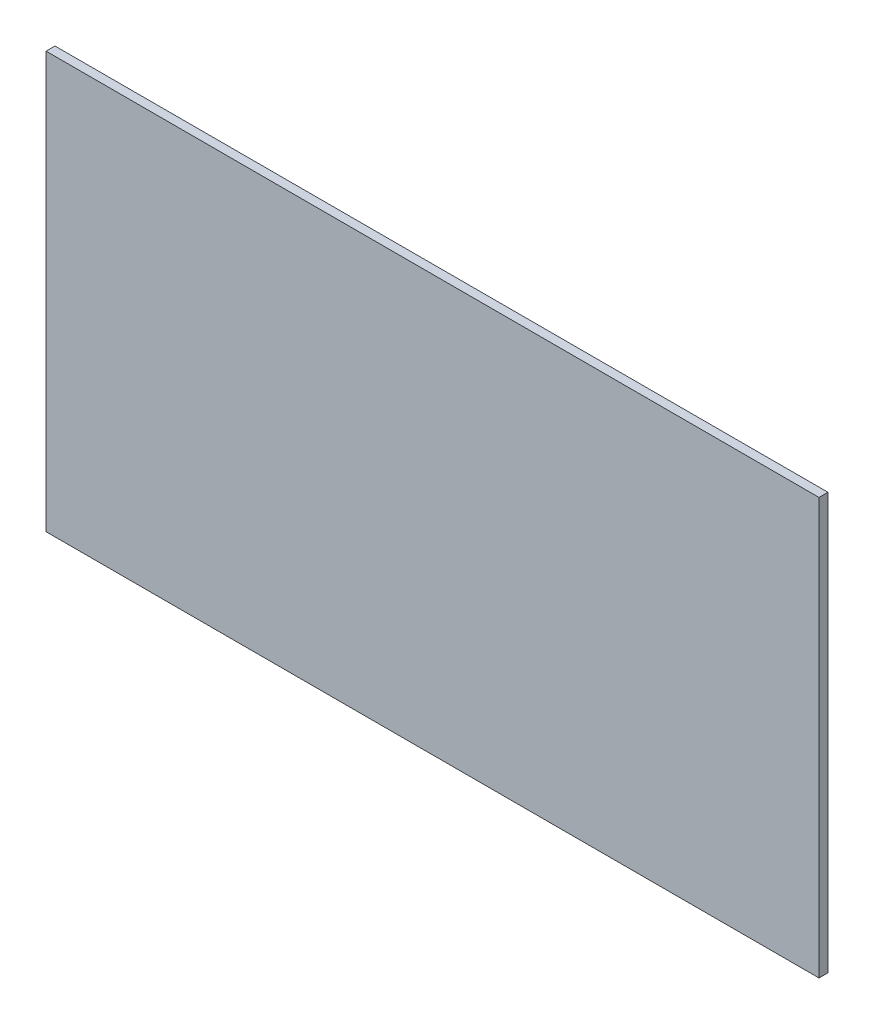
SolidWorks part; units mm, degrees
ref_plane "Front Plane" through (0, 0, 0) normal (0, 0, 1) x (1, 0, 0)
ref_plane "Top Plane" through (0, 0, 0) normal (0, 1, 0) x (1, 0, 0)
ref_plane "Right Plane" through (0, 0, 0) normal (1, 0, 0) x (0, 0, -1)
sketch "Sketch1" plane through (0, 0, 0) normal (0, 0, 1) x (1, 0, 0)
  line L1 (-65, -35) -> (65, -35)
  line L2 (-65, -35) -> (-65, 35)
  line L3 (-65, 35) -> (65, 35)
  line L4 (65, -35) -> (65, 35)
  line L5 (-65, -35) -> (65, 35) construction
  line L6 (-65, 35) -> (65, -35) construction
  point P0 (0, 0)
  dimension "D1" = 130
  dimension "D2" = 70
extrude "Boss-Extrude1" add sketch "Sketch1" along normal blind 1.5
